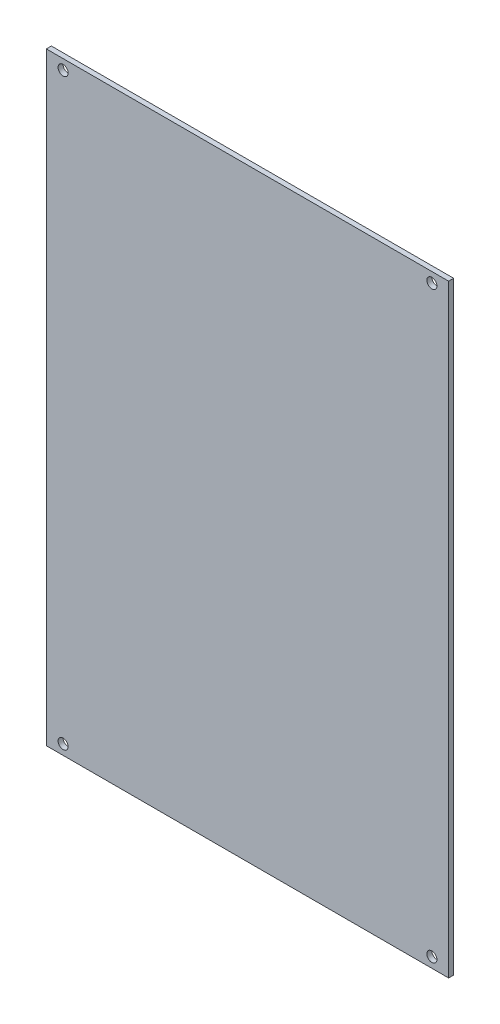
SolidWorks part; units mm, degrees
material "1060 合金"
ref_plane "前视基准面" through (0, 0, 0) normal (0, 0, 1) x (1, 0, 0)
ref_plane "上视基准面" through (0, 0, 0) normal (0, 1, 0) x (1, 0, 0)
ref_plane "右视基准面" through (0, 0, 0) normal (1, 0, 0) x (0, 0, -1)
sketch "草图1" plane through (0, 0, 0) normal (0, 0, 1) x (1, 0, 0)
  line L36 (3561.5693, 909.613) -> (3561.5693, -890.387)
  line L37 (3561.5693, 909.613) -> (4761.5693, 909.613)
  line L38 (4761.5693, 909.613) -> (4761.5693, -890.387)
  line L39 (3561.5693, -890.387) -> (4761.5693, -890.387)
  circle A52 centre (3611.5693, 879.613) radius 15
  circle A61 centre (4711.5693, 879.613) radius 15
  circle A62 centre (3611.5693, -860.387) radius 15
  circle A63 centre (4711.5693, -860.387) radius 15
  dimension "D76" = 30
  dimension "D77" = 30
  dimension "D78" = 50
  dimension "D80" = 50
  dimension "D81" = 30
  dimension "D20" = 1200
  dimension "D69" = 50
  dimension "D71" = 50
  dimension "D75" = 1800
  dimension "D79" = 30
extrude "凸台-拉伸1" add sketch "草图1" along normal blind 3
scale "缩放比例1" bodies to scale 101 104 102 103 108 scale about centroid uniform scaling no x scale factor 0.1 y scale factor 0.1 z scale factor 0.5
